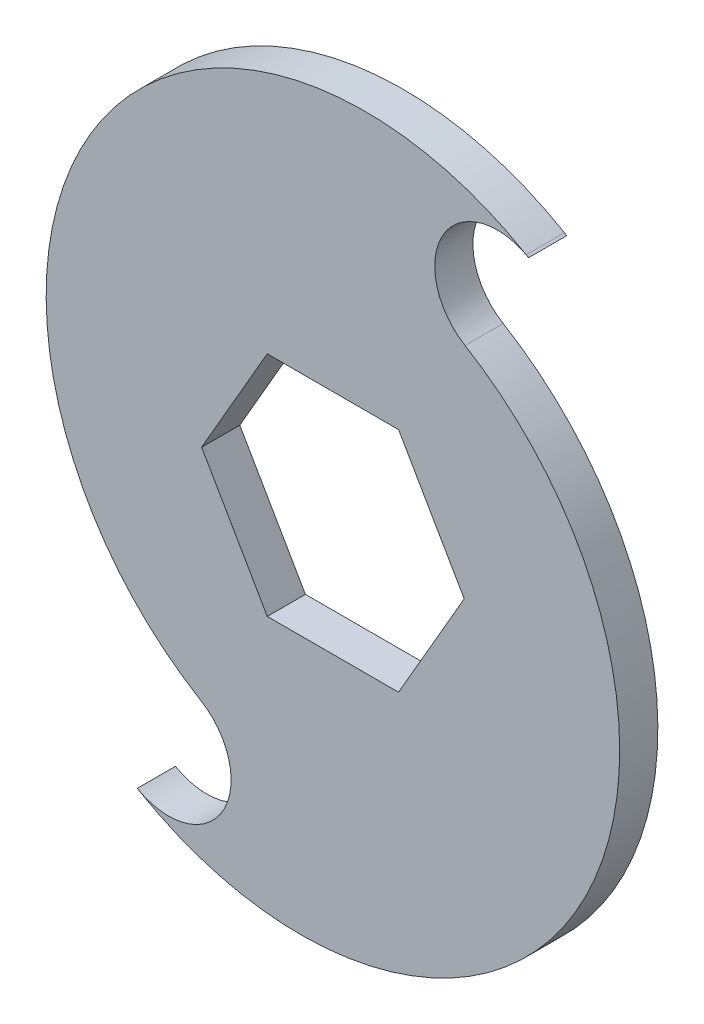
SolidWorks part; units mm, degrees
material "AISI 1020"
ref_plane "Frontal" through (0, 0, 0) normal (0, 0, 1) x (1, 0, 0)
ref_plane "Superior" through (0, 0, 0) normal (0, 1, 0) x (1, 0, 0)
ref_plane "Direito" through (0, 0, 0) normal (1, 0, 0) x (0, 0, -1)
sketch "Esboço1" plane through (0, 0, 0) normal (0, 0, 1) x (1, 0, 0)
  line L1 (17.205, 0) -> (8.6025, 14.9)
  line L2 (8.6025, 14.9) -> (-8.6025, 14.9)
  line L3 (-8.6025, 14.9) -> (-17.205, 0)
  line L4 (-17.205, 0) -> (-8.6025, -14.9)
  line L5 (-8.6025, -14.9) -> (8.6025, -14.9)
  line L6 (8.6025, -14.9) -> (17.205, 0)
  circle A0 centre (0, 0) radius 14.9 construction
  circle A1 centre (0, 0) radius 50
  dimension "D2" = 100
  dimension "D1" = 29.8
extrude "Ressalto-extrusão2" add sketch "Esboço1" along normal blind 5
sketch "Esboço2" plane through (0, 0, 5) normal (0, 0, 1) x (1, 0, 0)
  circle A0 centre (0, 0) radius 50 construction
  circle A1 centre (0, 0) radius 50
  arc A2 (-25.6807, -42.9018) -> (-17.3157, -28.7983) centre (-21.5406, -35.8249) ccw
  arc A3 (25.3328, 43.1074) -> (-17.3157, -28.7983) centre (4.2247, 7.0263) ccw
  arc A4 (25.6807, 42.9018) -> (17.3157, 28.7983) centre (21.5406, 35.8249) ccw
  circle A5 centre (0, 0) radius 50
  arc A6 (-25.3328, -43.1074) -> (17.3157, 28.7983) centre (-4.2247, -7.0263) ccw
  point P11 (0, 0)
  point P19 (-0.1739, 0.1028)
  point P25 (0, 0)
  dimension "D1" = 2
extrude "Corte-extrusão3" cut sketch "Esboço2" against normal blind 10 contours A6 A5 A4 | A3 A1 A2
